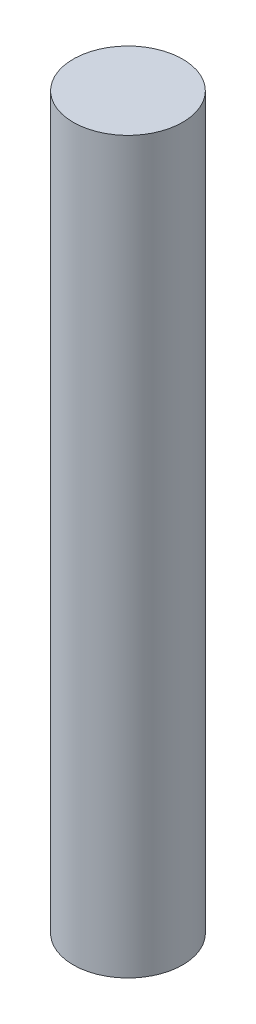
SolidWorks part; units mm, degrees
ref_plane "Front Plane" through (0, 0, 0) normal (0, 0, 1) x (1, 0, 0)
ref_plane "Top Plane" through (0, 0, 0) normal (0, 1, 0) x (1, 0, 0)
ref_plane "Right Plane" through (0, 0, 0) normal (1, 0, 0) x (0, 0, -1)
sketch "Sketch1" plane through (0, 0, 0) normal (0, 1, 0) x (1, 0, 0)
  circle A0 centre (0, 0) radius 15
  dimension "D1" = 30
extrude "Boss-Extrude1" add sketch "Sketch1" along normal blind 200
